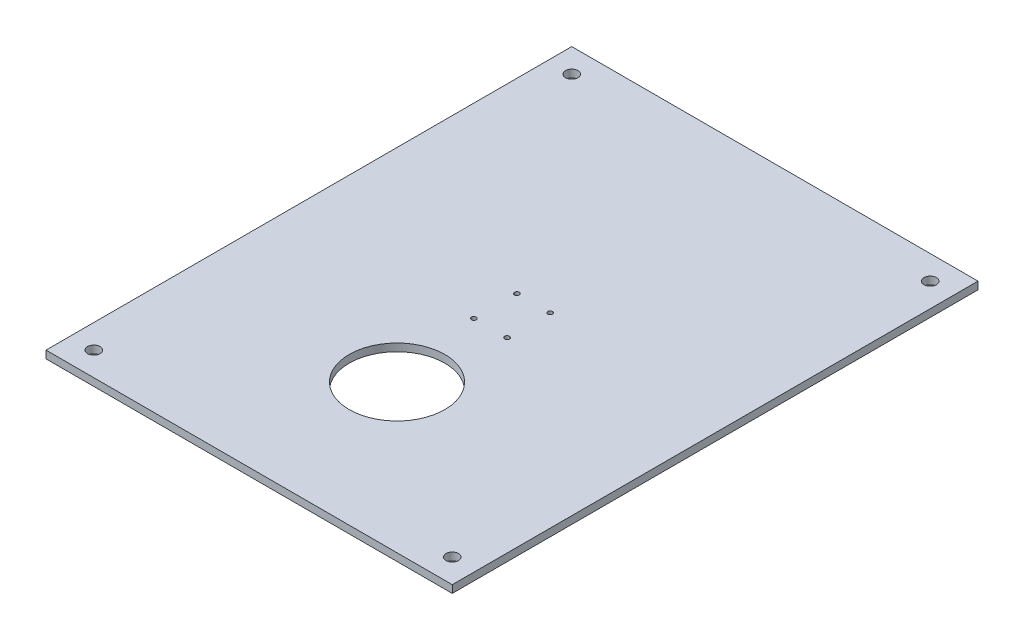
SolidWorks part; units mm, degrees
ref_plane "Front Plane" through (0, 0, 0) normal (0, 0, 1) x (1, 0, 0)
ref_plane "Top Plane" through (0, 0, 0) normal (0, 1, 0) x (1, 0, 0)
ref_plane "Right Plane" through (0, 0, 0) normal (1, 0, 0) x (0, 0, -1)
sketch "Sketch2" plane through (0, 0, 0) normal (0, 1, 0) x (1, 0, 0)
  line L0 (0, 61.8644) -> (0, -41.9492) construction
  line L1 (45.7627, 0) -> (-92.7966, 0) construction
  line L3 (85, -110) -> (-85, -110)
  line L4 (85, -110) -> (85, 110)
  line L5 (85, 110) -> (-85, 110)
  line L6 (-85, -110) -> (-85, 110)
  line L7 (85, -110) -> (-85, 110) construction
  line L8 (85, 110) -> (-85, -110) construction
  circle A0 centre (-75, 100) radius 2.6
  circle A1 centre (75, 100) radius 2.6
  circle A2 centre (75, -100) radius 2.6
  circle A3 centre (-75, -100) radius 2.6
  circle A4 centre (-6.9545, 9) radius 1
  circle A5 centre (6.9545, 9) radius 1
  circle A6 centre (6.9545, -9) radius 1
  circle A7 centre (-6.9545, -9) radius 1
  circle A8 centre (0, -48.1171) radius 20
  point P1 (0, 0)
  dimension "D3" = 10
  dimension "D4" = 9
  dimension "D1" = 170
  dimension "D2" = 220
  dimension "D5" = 10
extrude "Boss-Extrude1" add sketch "Sketch2" along normal blind 3.175
equation "\"connector_D1\" = 70 'the big holes diameter"
equation "\"mtg_hole_D\" = 5.5 'mounting holes"
equation "\"mtg_dfc\" = 40 'mounting hole distance from center"
equation "\"plate_thickness\" = 6.35 'thickness of the plate "
equation "\"t_height\" = 200"
equation "\"t_width\" = 240"
equation "\"t_length\" = 240"
equation "\"plate_hole_from_edge\" = 9"
equation "\"plate_spacing\" = 1"
equation "\"front_plate_height\" = \"t_height\" + 38"
equation "\"front_plate_width\" = \"t_width\" + 38"
equation "\"side_plate_height\" = \"front_plate_height\""
equation "\"side_plate_length\" = \"t_length\" + 38"
equation "\"top_plate_width\" = \"front_plate_width\""
equation "\"top_plate_length\" = \"side_plate_length\""
equation "\"itx_support_t_slot_length\" = \"t_width\" + (2 * 20.5)"
equation "\"locomotion_length\" = \"t_length\""
equation "\"locomotion_width\" = \"t_width\""
equation "\"locomotion_height\" = 40"
equation "\"itx_mtg_hole_spacing\" = 40"
equation "\"emg30_bracket_hole_len\" = 60"
equation "\"emg30_bracket_hole_wid\" = 11"
equation "\"perce_t_height\" = 50"
equation "\"perce_top_width\" = 170"
equation "\"perce_mtg_hole_spacing\" = \"perce_top_width\" - 20"
equation "\"D1@Sketch2\"=\"perce_top_width\""
equation "\"D1@Boss-Extrude1\"=.125in"
